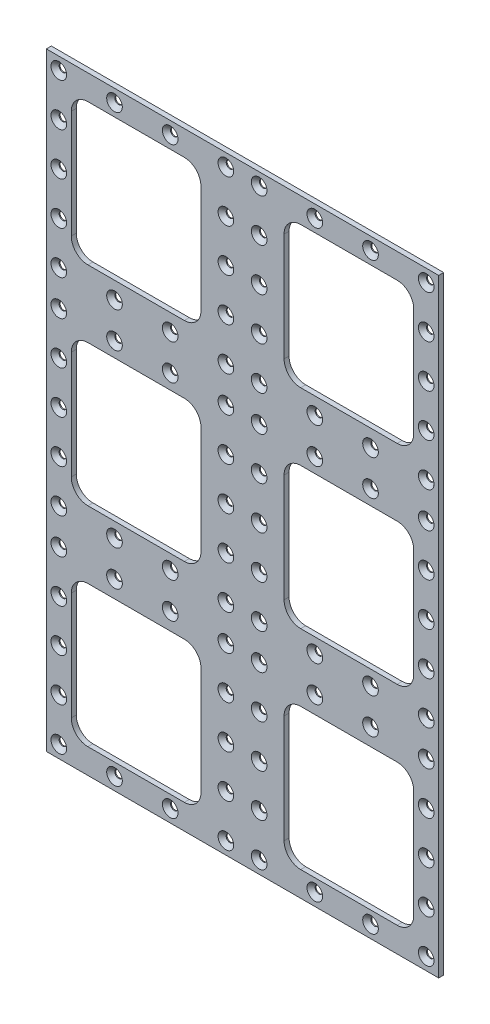
SolidWorks part; units mm, degrees
material "6061-T6 (SS)"
ref_plane "Alzado" through (0, 0, 0) normal (0, 0, 1) x (1, 0, 0)
ref_plane "Planta" through (0, 0, 0) normal (0, 1, 0) x (1, 0, 0)
ref_plane "Vista lateral" through (0, 0, 0) normal (1, 0, 0) x (0, 0, -1)
sketch "Sketch1" plane through (0, 0, 0) normal (0, 0, 1) x (1, 0, 0)
  line L1 (-118, 183) -> (118, 183)
  line L2 (-118, 183) -> (-118, -183)
  line L3 (-118, -183) -> (118, -183)
  line L4 (118, 183) -> (118, -183)
  line L5 (-118, 183) -> (118, -183) construction
  line L6 (-118, -183) -> (118, 183) construction
  point P0 (0, 0)
  dimension "D1" = 366
  dimension "D2" = 236
extrude "Boss-Extrude1" add sketch "Sketch1" along normal blind 3
sketch "Sketch2" plane through (0, 0, 0) normal (0, 0, 1) x (1, 0, 0)
  line L0 (0, 186.1376) -> (0, -191.1438) construction
  line L1 (-164.2926, 0) -> (162.9273, 0) construction
  line L2 (118, 183) -> (-118, 183) construction
  line L3 (-103, 168) -> (-25, 168)
  line L4 (-103, 168) -> (-103, 83)
  line L5 (-103, 83) -> (-25, 83)
  line L6 (-25, 168) -> (-25, 83)
  line L7 (-103, 168) -> (-25, 83) construction
  line L8 (-103, 83) -> (-25, 168) construction
  line L9 (-118, 183) -> (-118, -183) construction
  point P5 (-64, 125.5)
  dimension "D1" = 15
  dimension "D2" = 15
  dimension "D3" = 78
  dimension "D4" = 85
extrude "Cut-Extrude4" cut sketch "Sketch2" along normal through all
fillet "Fillet1" radius 10 4 edges at (-25, 83, 1.5) (-25, 168, 1.5) (-103, 83, 1.5) (-103, 168, 1.5)
pattern_linear "LPattern1" count 3 spacing 125.5 along (0, -1, 0) count 2 spacing 128 along (1, 0, 0) of "Cut-Extrude4", "Fillet1"
sketch "Sketch7" plane through (0, 0, 3) normal (0, 0, 1) x (1, 0, 0)
  line L0 (-118, 183) -> (-118, -183) construction
  line L1 (118, 183) -> (-118, 183) construction
  point P0 (-110.5, 175.5)
  dimension "D1" = 7.5
  dimension "D2" = 7.5
hole_wizard "CSK for M4 Flat Head Machine Screw3" positions "Sketch7" profile "Sketch8" countersink size "M4" standard "ANSI Metric" end condition through all
sketch "Sketch8" plane through (-110.5, 175.5, 3) normal (1, 0, 0) x (0, -1, 0)
  line L0 (0, 0) -> (0, 3)
  line L1 (0, 3) -> (2.25, 3)
  line L2 (2.25, 3) -> (2.25, 2.45)
  line L3 (2.25, 2.45) -> (4.7, 0)
  line L5 (4.7, 0) -> (0, 0)
  line L6 (-2.25, 2.45) -> (-4.7, 0) construction
  line L11 (0, -6.35) -> (0, 107.95) construction
  dimension "Thru Hole Dia." = 4.5
  dimension "Thru Hole Depth" = 3
  dimension "Near C'Sink Dia." = 9.4
  dimension "Near C'Sink Angle" = 90
sketch "Sketch9" plane through (0, 0, 3) normal (0, 0, 1) x (1, 0, 0)
  line L0 (0, 183) -> (0, -183) construction
  line L1 (118, 183) -> (-118, 183) construction
  line L2 (-118, -183) -> (118, -183) construction
  line L3 (-118, 62.75) -> (118, 62.75) construction
  line L4 (-118, -62.75) -> (118, -62.75) construction
  line L5 (-93, 83) -> (-35, 83) construction
  line L6 (-118, 183) -> (-118, -183) construction
  line L7 (118, -183) -> (118, 183) construction
  line L8 (-35, 42.5) -> (-93, 42.5) construction
  line L9 (-93, -42.5) -> (-35, -42.5) construction
  line L10 (-35, -83) -> (-93, -83) construction
pattern_linear "LPattern5" count 4 spacing 33.5 along (1, 0, 0) count 5 spacing 25.6875 along (0, -1, 0) skipping (1, 1), (1, 2), (1, 3), (2, 1), (2, 2), (2, 3) of "CSK for M4 Flat Head Machine Screw3"
pattern_linear "LPattern6" count 3 spacing 124.125 along (0, -1, 0) of "LPattern5", "CSK for M4 Flat Head Machine Screw3"
mirror "Mirror1" about plane through (0, 0, 0) normal (1, 0, 0) of "LPattern6", "CSK for M4 Flat Head Machine Screw3", "LPattern5"
